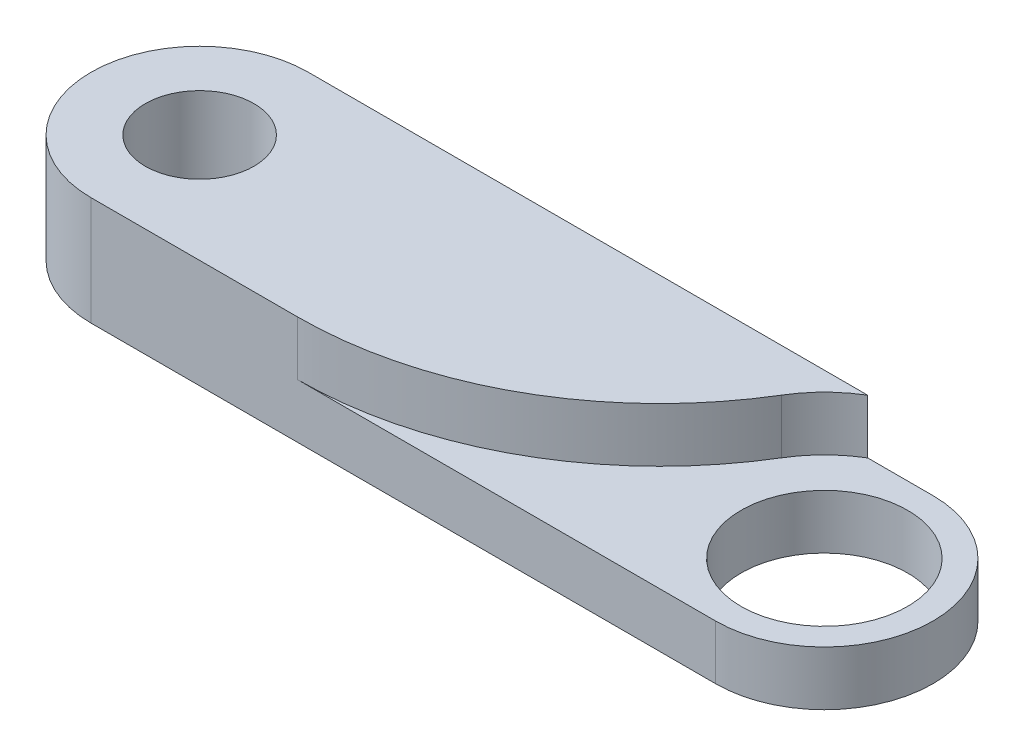
SolidWorks part; units mm, degrees
material "ABS"
ref_plane "正面" through (0, 0, 0) normal (0, 0, 1) x (1, 0, 0)
ref_plane "平面" through (0, 0, 0) normal (0, 1, 0) x (1, 0, 0)
ref_plane "右側面" through (0, 0, 0) normal (1, 0, 0) x (0, 0, -1)
sketch "ｽｹｯﾁ1" plane through (0, 0, 0) normal (0, 1, 0) x (1, 0, 0)
  line L0 (-17.25, 0) -> (17.25, 0) construction
  line L1 (-17.25, 6) -> (17.25, 6)
  line L2 (-17.25, -6) -> (17.25, -6)
  arc A0 (-17.25, 6) -> (-17.25, -6) centre (-17.25, 0) ccw
  arc A1 (17.25, -6) -> (17.25, 6) centre (17.25, 0) ccw
  circle A2 centre (-17.25, 0) radius 3
  circle A3 centre (17.25, 0) radius 4.6
  point P2 (0, 0)
  dimension "D2" = 6
  dimension "D3" = 6
  dimension "D4" = 9.2
  dimension "D1" = 34.5
extrude "ﾎﾞｽ - 押し出し1" add sketch "ｽｹｯﾁ1" along normal blind 6
sketch "ｽｹｯﾁ3" plane through (0, 6, 0) normal (0, 1, 0) x (1, 0, 0)
  circle A0 centre (17.25, 0) radius 7
  circle A1 centre (17.25, 0) radius 4.6 construction
  dimension "D1" = 14
extrude "ｶｯﾄ - 押し出し1" cut sketch "ｽｹｯﾁ3" against normal blind 3
fillet "ﾌｨﾚｯﾄ1" radius 20 1 edges at (13.6444, 4.5, 6)
